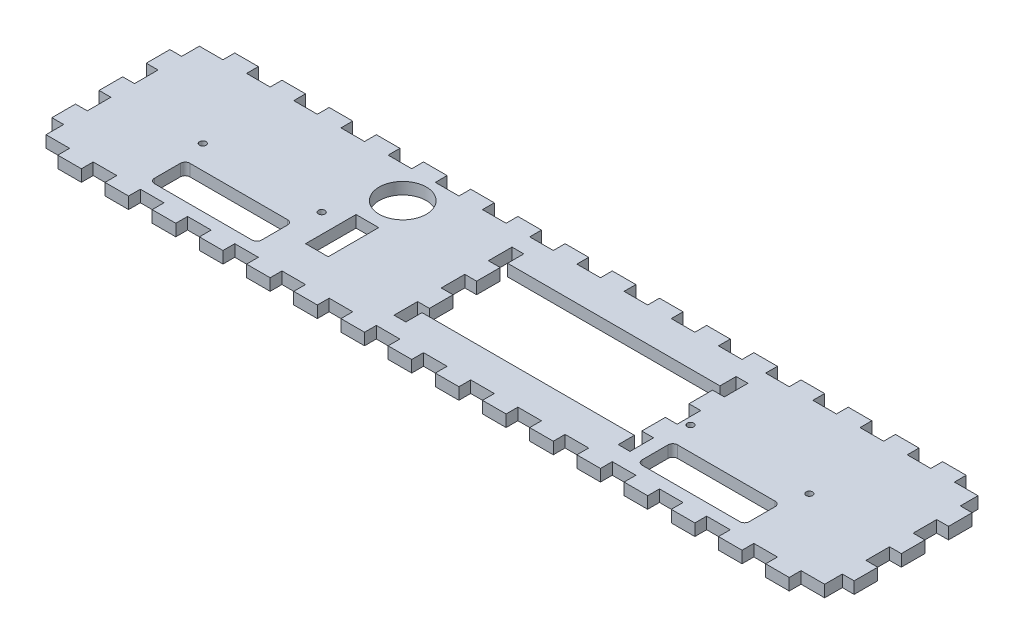
SolidWorks part; units mm, degrees
material "Pine"
ref_plane "Front Plane" through (0, 0, 0) normal (0, 0, 1) x (1, 0, 0)
ref_plane "Top Plane" through (0, 0, 0) normal (0, 1, 0) x (1, 0, 0)
ref_plane "Right Plane" through (0, 0, 0) normal (1, 0, 0) x (0, 0, -1)
sketch "Sketch1" plane through (0, 0, 0) normal (0, 1, 0) x (1, 0, 0)
  line L1 (0, 0) -> (431.8, 0)
  line L2 (0, 0) -> (0, 95.25)
  line L3 (0, 95.25) -> (431.8, 95.25)
  line L4 (431.8, 0) -> (431.8, 95.25)
  dimension "D1" = 431.8
  dimension "D2" = 95.25
extrude "Boss-Extrude1" add sketch "Sketch1" along normal blind 6.35
sketch "Sketch2" plane through (0, 6.35, 0) normal (0, 1, 0) x (1, 0, 0)
  line L1 (431.8, 95.25) -> (0, 95.25) construction
  line L2 (6.35, 95.25) -> (19.05, 95.25)
  line L3 (6.35, 95.25) -> (6.35, 88.9)
  line L4 (6.35, 88.9) -> (19.05, 88.9)
  line L7 (19.05, 95.25) -> (19.05, 88.9)
  line L8 (0, 0) -> (431.8, 0) construction
  line L9 (6.35, 0) -> (19.05, 0)
  line L10 (6.35, 0) -> (6.35, 6.35)
  line L11 (6.35, 6.35) -> (19.05, 6.35)
  line L12 (19.05, 0) -> (19.05, 6.35)
  line L13 (0, 95.25) -> (0, 0) construction
  dimension "D1" = 6.35
  dimension "D2" = 12.7
  dimension "D3" = 6.35
extrude "Cut-Extrude1" cut sketch "Sketch2" against normal through all
pattern_linear "LPattern1" count 17 spacing 25.4 along (1, 0, 0) of "Cut-Extrude1"
sketch "Sketch3" plane through (0, 6.35, 0) normal (0, 1, 0) x (1, 0, 0)
  line L1 (6.35, 88.9) -> (0, 88.9)
  line L2 (6.35, 88.9) -> (6.35, 95.25)
  line L3 (6.35, 95.25) -> (0, 95.25)
  line L4 (0, 88.9) -> (0, 95.25)
  line L5 (6.35, 6.35) -> (0, 6.35)
  line L6 (6.35, 6.35) -> (6.35, 0)
  line L7 (6.35, 0) -> (0, 0)
  line L8 (0, 6.35) -> (0, 0)
  line L9 (425.45, 88.9) -> (431.8, 88.9)
  line L10 (425.45, 88.9) -> (425.45, 95.25)
  line L11 (425.45, 95.25) -> (431.8, 95.25)
  line L12 (431.8, 88.9) -> (431.8, 95.25)
  line L13 (425.45, 6.35) -> (431.8, 6.35)
  line L14 (425.45, 6.35) -> (425.45, 0)
  line L15 (425.45, 0) -> (431.8, 0)
  line L16 (431.8, 6.35) -> (431.8, 0)
extrude "Cut-Extrude2" cut sketch "Sketch3" against normal through all
sketch "Sketch5" plane through (0, 6.35, 0) normal (0, 1, 0) x (1, 0, 0)
  line L0 (311.15, 88.9) -> (311.15, 6.35) construction
  line L1 (190.5, 88.9) -> (190.5, 6.35) construction
  line L2 (184.15, 88.9) -> (196.85, 88.9) construction
  line L3 (196.85, 6.35) -> (184.15, 6.35) construction
  line L5 (190.5, 53.975) -> (184.15, 53.975)
  line L6 (190.5, 53.975) -> (190.5, 41.275)
  line L7 (190.5, 41.275) -> (184.15, 41.275)
  line L8 (184.15, 53.975) -> (184.15, 41.275)
  line L9 (311.15, 53.975) -> (304.8, 53.975)
  line L10 (311.15, 53.975) -> (311.15, 41.275)
  line L11 (311.15, 41.275) -> (304.8, 41.275)
  line L12 (304.8, 53.975) -> (304.8, 41.275)
  point P18 (190.5, 47.625)
  point P19 (311.15, 47.625)
  dimension "D1" = 6.35
  dimension "D2" = 12.7
extrude "Cut-Extrude4" cut sketch "Sketch5" against normal through all
pattern_linear "LPattern2" count 2 spacing 25.4 along (0, 0, -1) count 2 spacing 25.4 along (0, 0, 1) of "Cut-Extrude4"
sketch "Sketch6" plane through (0, 6.35, 0) normal (0, 1, 0) x (1, 0, 0)
  line L0 (190.5, 47.625) -> (304.8, 47.625) construction
  line L1 (190.5, 41.275) -> (190.5, 53.975) construction
  line L2 (304.8, 53.975) -> (304.8, 41.275) construction
  line L4 (304.8, 24.6063) -> (190.5, 24.6062)
  line L5 (304.8, 24.6063) -> (304.8, 70.6438)
  line L6 (304.8, 70.6438) -> (190.5, 70.6437)
  line L7 (190.5, 24.6062) -> (190.5, 70.6437)
  line L8 (304.8, 24.6063) -> (190.5, 70.6437) construction
  line L9 (304.8, 70.6438) -> (190.5, 24.6062) construction
  point P6 (247.65, 47.625)
  dimension "D1" = 46.0375
  dimension "D2" = 114.3
extrude "Cut-Extrude5" cut sketch "Sketch6" against normal through all
sketch "Sketch7" plane through (0, 6.35, 0) normal (0, 1, 0) x (1, 0, 0)
  line L0 (0, 44.45) -> (431.8, 44.45) construction
  line L1 (0, 88.9) -> (0, 6.35) construction
  line L2 (431.8, 6.35) -> (431.8, 88.9) construction
  line L3 (323.85, 0) -> (336.55, 0) construction
  circle A0 centre (52.65, 44.45) radius 1.75
  circle A1 centre (116.65, 44.45) radius 1.75
  circle A2 centre (315.15, 44.45) radius 1.75
  circle A3 centre (379.15, 44.45) radius 1.75
  dimension "D6" = 3.5
  dimension "D1" = 44.45
  dimension "D2" = 64
  dimension "D3" = 64
  dimension "D4" = 116.65
  dimension "D5" = 116.65
extrude "Cut-Extrude6" cut sketch "Sketch7" against normal through all
sketch "Sketch8" plane through (0, 6.35, 0) normal (0, 1, 0) x (1, 0, 0)
  line L0 (0, 88.9) -> (0, 6.35) construction
  line L1 (0, 88.9) -> (6.35, 88.9)
  line L2 (0, 88.9) -> (0, 79.375)
  line L3 (0, 79.375) -> (6.35, 79.375)
  line L4 (6.35, 88.9) -> (6.35, 79.375)
  line L5 (0, 6.35) -> (6.35, 6.35)
  line L6 (0, 6.35) -> (0, 15.875)
  line L7 (0, 15.875) -> (6.35, 15.875)
  line L8 (6.35, 6.35) -> (6.35, 15.875)
  line L9 (0, 28.575) -> (6.35, 28.575)
  line L10 (0, 28.575) -> (0, 41.275)
  line L11 (0, 41.275) -> (6.35, 41.275)
  line L12 (6.35, 28.575) -> (6.35, 41.275)
  line L13 (190.5, 53.975) -> (184.15, 53.975) construction
  line L14 (0, 66.675) -> (6.35, 66.675)
  line L15 (0, 66.675) -> (0, 53.975)
  line L16 (0, 53.975) -> (6.35, 53.975)
  line L17 (6.35, 66.675) -> (6.35, 53.975)
  line L18 (184.15, 41.275) -> (190.5, 41.275) construction
  line L19 (190.5, 28.575) -> (184.15, 28.575) construction
  line L20 (19.05, 0) -> (19.05, 6.35) construction
  line L21 (190.5, 79.375) -> (184.15, 79.375) construction
  line L22 (184.15, 15.875) -> (190.5, 15.875) construction
extrude "Cut-Extrude7" cut sketch "Sketch8" against normal through all
pattern_linear "LPattern3" count 2 spacing 425.45 along (1, 0, 0) of "Cut-Extrude7"
sketch "Sketch9" plane through (0, 6.35, 0) normal (0, 1, 0) x (1, 0, 0)
  line L0 (0, 53.975) -> (0, 41.275) construction
  line L1 (127, 25.4) -> (139.192, 25.4)
  line L2 (127, 25.4) -> (127, 52.578)
  line L3 (127, 52.578) -> (139.192, 52.578)
  line L4 (139.192, 25.4) -> (139.192, 52.578)
  line L5 (120.65, 0) -> (133.35, 0) construction
  line L6 (133.096, 71.628) -> (133.096, 52.578) construction
  circle A0 centre (133.096, 71.628) radius 12.7
  dimension "D5" = 25.4
  dimension "D1" = 12.192
  dimension "D2" = 27.178
  dimension "D3" = 127
  dimension "D4" = 25.4
  dimension "D6" = 19.05
extrude "Cut-Extrude8" cut sketch "Sketch9" against normal through all
sketch "Sketch10" plane through (0, 6.35, 0) normal (0, 1, 0) x (1, 0, 0)
  line L0 (52.65, 44.45) -> (116.65, 44.45) construction
  line L1 (55.825, 31.75) -> (113.475, 31.75)
  line L2 (55.825, 31.75) -> (55.825, 12.7)
  line L3 (55.825, 12.7) -> (113.475, 12.7)
  line L4 (113.475, 31.75) -> (113.475, 12.7)
  line L5 (318.325, 31.75) -> (375.975, 31.75)
  line L6 (318.325, 31.75) -> (318.325, 12.7)
  line L7 (318.325, 12.7) -> (375.975, 12.7)
  line L8 (375.975, 31.75) -> (375.975, 12.7)
  line L9 (69.85, 6.35) -> (57.15, 6.35) construction
  line L10 (374.65, 6.35) -> (361.95, 6.35) construction
  circle A1 centre (315.15, 44.45) radius 1.75 construction
  circle A2 centre (379.15, 44.45) radius 1.75 construction
  dimension "D5" = 3.175
  dimension "D1" = 3.175
  dimension "D2" = 3.175
  dimension "D3" = 19.05
  dimension "D4" = 6.35
  dimension "D6" = 3.175
  dimension "D7" = 19.05
  dimension "D8" = 6.35
extrude "Cut-Extrude9" cut sketch "Sketch10" against normal through all
fillet "Fillet1" radius 2.54 8 edges at (318.325, 3.175, -31.75) (375.975, 3.175, -31.75) (375.975, 3.175, -12.7) (318.325, 3.175, -12.7) (55.825, 3.175, -12.7) (113.475, 3.175, -12.7) (113.475, 3.175, -31.75) (55.825, 3.175, -31.75)
